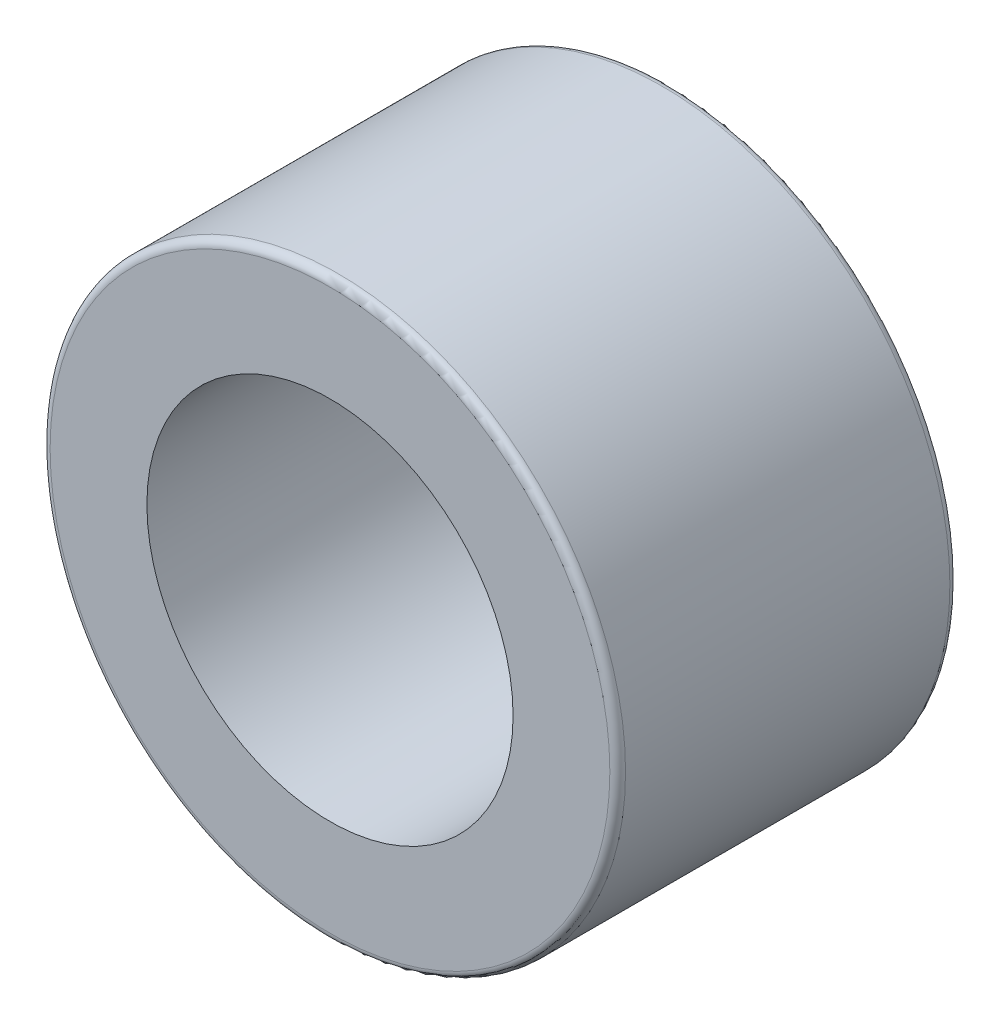
SolidWorks part; units mm, degrees
material "AISI 4340 Steel, annealed"
ref_plane "Front Plane" through (0, 0, 0) normal (0, 0, 1) x (1, 0, 0)
ref_plane "Top Plane" through (0, 0, 0) normal (0, 1, 0) x (1, 0, 0)
ref_plane "Right Plane" through (0, 0, 0) normal (1, 0, 0) x (0, 0, -1)
sketch "Sketch1" plane through (0, 0, 0) normal (0, 0, 1) x (1, 0, 0)
  circle A0 centre (0, 0) radius 7
  circle A1 centre (0, 0) radius 11
  dimension "D1" = 14
  dimension "D2" = 22
extrude "Boss-Extrude1" add sketch "Sketch1" along normal blind 13
fillet "Fillet1" radius 0.3 2 edges at (11, 0, 13) (11, 0, 0)
